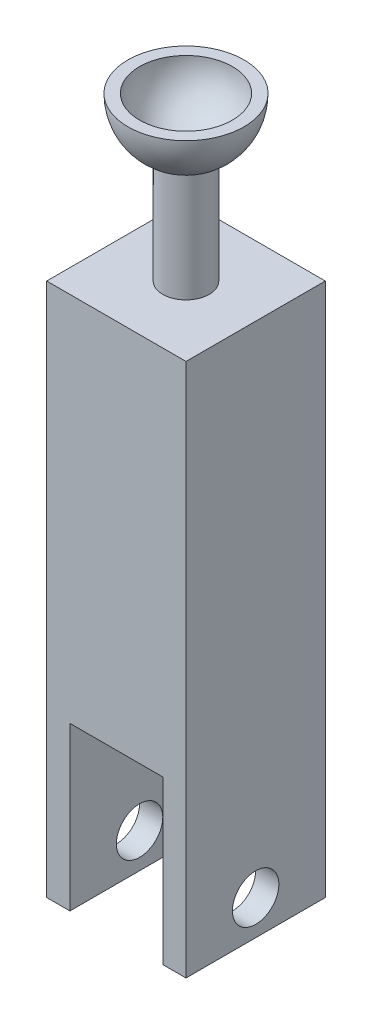
SolidWorks part; units mm, degrees
ref_plane "Alzado" through (0, 0, 0) normal (0, 0, 1) x (1, 0, 0)
ref_plane "Planta" through (0, 0, 0) normal (0, 1, 0) x (1, 0, 0)
ref_plane "Vista lateral" through (0, 0, 0) normal (1, 0, 0) x (0, 0, -1)
sketch "Croquis1" plane through (0, 0, 0) normal (0, 1, 0) x (1, 0, 0)
  line L1 (-30, -30) -> (30, -30)
  line L2 (-30, -30) -> (-30, 30)
  line L3 (-30, 30) -> (30, 30)
  line L4 (30, -30) -> (30, 30)
  line L5 (-30, -30) -> (30, 30) construction
  line L6 (-30, 30) -> (30, -30) construction
  point P0 (0, 0)
  dimension "D1" = 60
  dimension "D2" = 60
extrude "Saliente-Extruir1" add sketch "Croquis1" along normal blind 300
sketch "Croquis2" plane through (0, 0, 0) normal (0, 0, 1) x (1, 0, 0)
  line L1 (-20, 70) -> (20, 70)
  line L2 (-20, 70) -> (-20, 0)
  line L3 (-20, 0) -> (20, 0)
  line L4 (20, 70) -> (20, 0)
  dimension "D1" = 40
  dimension "D2" = 70
extrude "Cortar-Extruir1" cut sketch "Croquis2" against normal through all both and the other way through all
sketch "Croquis3" plane through (0, 0, 0) normal (1, 0, 0) x (0, 0, -1)
  line L0 (0, 0) -> (0, 15) construction
  circle A0 centre (0, 15) radius 10
  dimension "D1" = 20
  dimension "D2" = 15
extrude "Cortar-Extruir2" cut sketch "Croquis3" against normal through all both and the other way through all
sketch "Croquis4" plane through (0, 0, 0) normal (0, 0, 1) x (1, 0, 0)
  line L0 (-30, 300) -> (30, 300) construction
  line L1 (0, 300) -> (0, 230) construction
  line L2 (-10, 230) -> (-10, 277.0871)
  line L3 (-10, 230) -> (-30, 230)
  line L4 (-30, 300) -> (-30, 0) construction
  line L6 (0, 300) -> (-25, 300)
  line L7 (0, 300) -> (0, 280)
  line L10 (-25, 300) -> (-59.4005, 300)
  line L11 (-59.4005, 300) -> (-59.4005, 230)
  line L12 (-59.4005, 230) -> (-30, 230)
  arc A0 (-20, 300) -> (0, 280) centre (0, 300) ccw
  arc A1 (-25, 300) -> (-10, 277.0871) centre (0, 300) ccw
  circle A2 centre (0, 300) radius 25 construction
  circle A3 centre (0, 300) radius 20 construction
  dimension "D2" = 40
  dimension "D3" = 20
  dimension "D4" = 70
  dimension "D1" = 5
revolve "Cortar-Revolución5" cut sketch "Croquis4" angle 360 about L1
